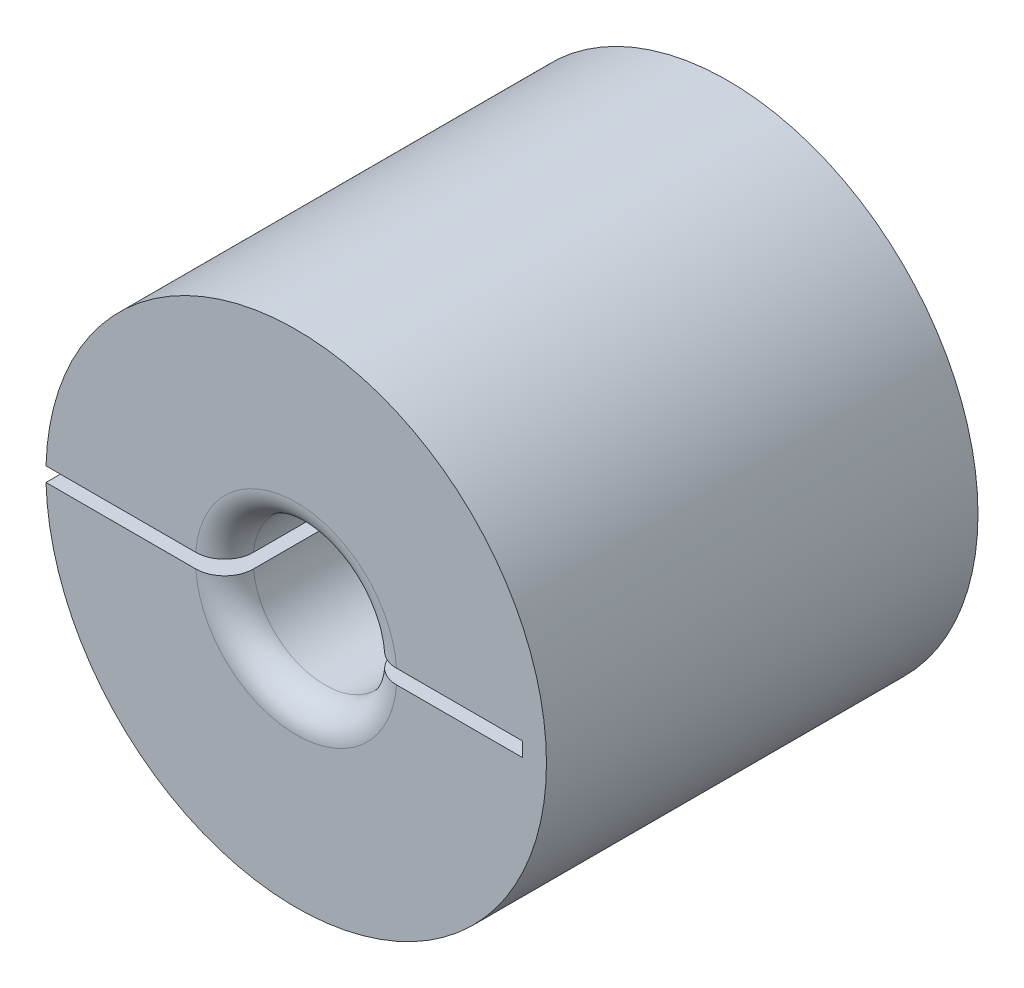
SolidWorks part; units mm, degrees
material "Copper"
ref_plane "Front Plane" through (0, 0, 0) normal (0, 0, 1) x (1, 0, 0)
ref_plane "Top Plane" through (0, 0, 0) normal (0, 1, 0) x (1, 0, 0)
ref_plane "Right Plane" through (0, 0, 0) normal (1, 0, 0) x (0, 0, -1)
sketch "Sketch1" plane through (0, 0, 0) normal (0, 0, 1) x (1, 0, 0)
  circle A0 centre (0, 0) radius 11.049
  circle A1 centre (0, 0) radius 3.175
extrude "Boss-Extrude1" add sketch "Sketch1" along normal blind 19.05
fillet "Fillet1" radius 1.27 2 edges at (3.175, 0, 0) (3.175, 0, 19.05)
sketch "Sketch3" plane through (0, 0, 19.05) normal (0, 0, 1) x (1, 0, 0)
  line L0 (11.049, 0) -> (-19.812, 0)
  line L2 (-11.549, -0.3175) -> (9.9809, -0.3175)
  line L3 (-11.549, -0.3175) -> (-11.549, 0.3175)
  line L4 (-11.549, 0.3175) -> (9.9809, 0.3175)
  line L5 (9.9809, -0.3175) -> (9.9809, 0.3175)
  circle A0 centre (0, 0) radius 11.049 construction
  dimension "D1" = 0.635
  dimension "D2" = 0.3175
extrude "Cut-Extrude1" cut sketch "Sketch3" against normal through all contours L4 L5 L2 L3
